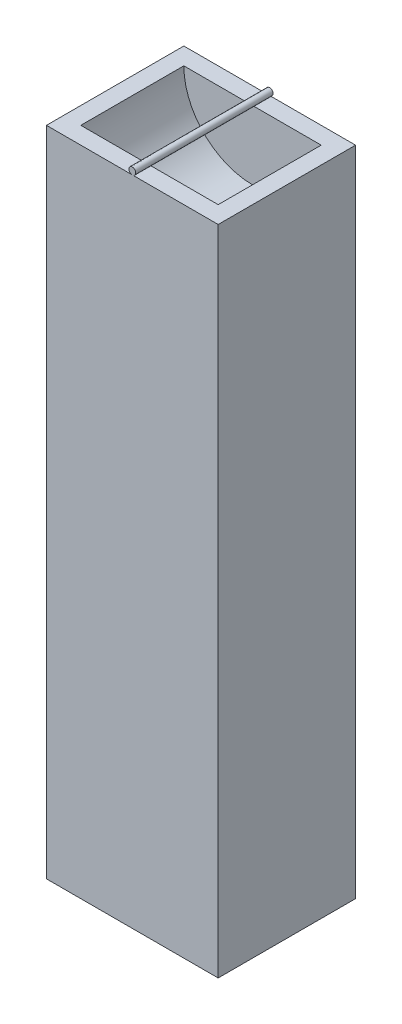
SolidWorks part; units mm, degrees
ref_plane "Front Plane" through (0, 0, 0) normal (0, 0, 1) x (1, 0, 0)
ref_plane "Top Plane" through (0, 0, 0) normal (0, 1, 0) x (1, 0, 0)
ref_plane "Right Plane" through (0, 0, 0) normal (1, 0, 0) x (0, 0, -1)
sketch "Sketch1" plane through (0, 0, 0) normal (0, 0, 1) x (1, 0, 0)
  line L1 (-50.4211, 49.8118) -> (-25.4211, 49.8118)
  line L2 (-50.4211, 49.8118) -> (-50.4211, -45.1882)
  line L3 (-50.4211, -45.1882) -> (-25.4211, -45.1882)
  line L4 (-25.4211, 49.8118) -> (-25.4211, -45.1882)
  point P4 (0, 0)
  dimension "D1" = 95
  dimension "D2" = 25
extrude "Boss-Extrude1" add sketch "Sketch1" along normal mid plane 20
sketch "Sketch2" plane through (0, 0, 0) normal (0, 0, 1) x (1, 0, 0)
  line L0 (-25.4211, 49.8118) -> (-50.4211, 49.8118) construction
  circle A0 centre (-37.9211, 49.8118) radius 10
  dimension "D1" = 20
extrude "Cut-Extrude1" cut sketch "Sketch2" against normal mid plane 15
ref_plane "Plane1" through (-37.9211, 0, 0) normal (-1, 0, 0) x (0, 0, 1)
sketch "Sketch4" plane through (-37.9211, 0, 0) normal (-1, 0, 0) x (0, 0, 1)
  line L0 (-10, 50.31) -> (10, 50.31)
sweep "Sweep1" add path "Sketch4" circular profile diameter 1 parameters "D3"=1
